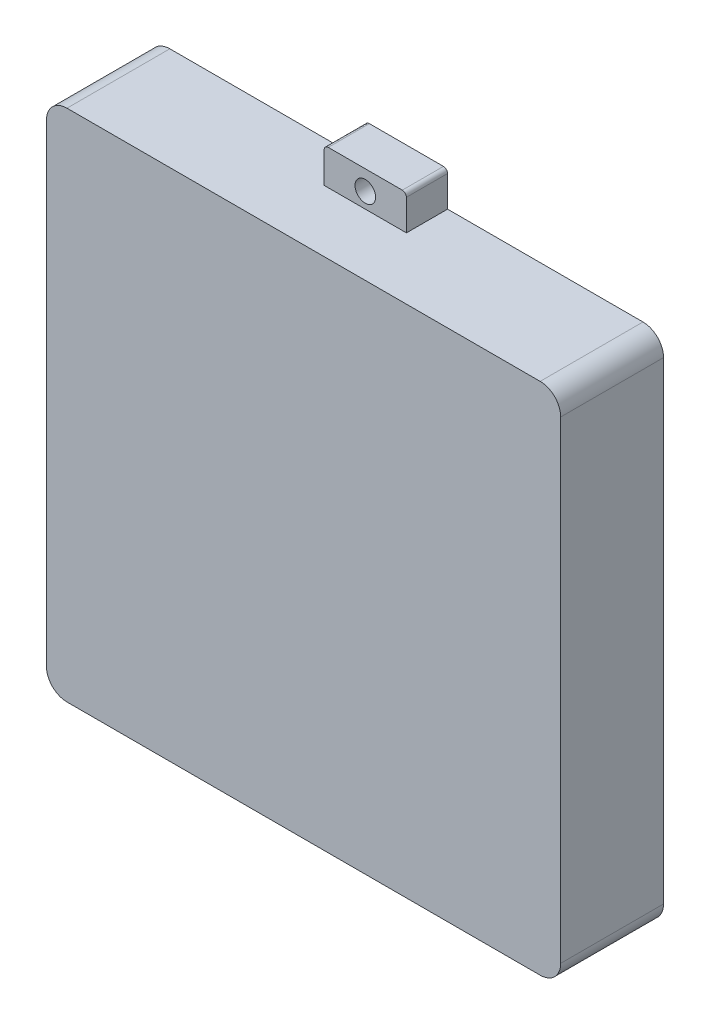
SolidWorks part; units mm, degrees
ref_plane "Front Plane" through (0, 0, 0) normal (0, 0, 1) x (1, 0, 0)
ref_plane "Top Plane" through (0, 0, 0) normal (0, 1, 0) x (1, 0, 0)
ref_plane "Right Plane" through (0, 0, 0) normal (1, 0, 0) x (0, 0, -1)
sketch "Sketch1" plane through (0, 0, 0) normal (0, 0, 1) x (1, 0, 0)
  line L1 (0, 0) -> (250, 0)
  line L2 (0, 0) -> (0, 250)
  line L3 (0, 250) -> (250, 250)
  line L4 (250, 0) -> (250, 250)
  dimension "D1" = 250
  dimension "D2" = 250
extrude "Boss-Extrude1" add sketch "Sketch1" along normal blind 50
sketch "Sketch2" plane through (0, 0, 0) normal (0, 0, 1) x (1, 0, 0)
  line L0 (0, 0) -> (250, 0) construction
  line L2 (105, 0) -> (105, -15)
  line L3 (107, -17) -> (143, -17)
  line L4 (145, 0) -> (145, -15)
  line L5 (0, 0) -> (250, 0) construction
  line L7 (145, 0) -> (105, 0)
  arc A0 (145, -15) -> (143, -17) centre (143, -15) cw
  arc A1 (107, -17) -> (105, -15) centre (107, -15) cw
  point P12 (125, 0)
  point P13 (125, -17)
  dimension "D1" = 2
  dimension "D2" = 20
  dimension "D3" = 15
  dimension "D4" = 20
extrude "Boss-Extrude2" add sketch "Sketch2" along normal blind 20
ref_plane "Plane1" through (0, 125, 0) normal (0, 1, 0) x (1, 0, 0)
mirror "Mirror1" about plane through (0, 125, 0) normal (0, 1, 0) of "Boss-Extrude2"
sketch "Sketch3" plane through (0, 0, 0) normal (0, 0, -1) x (-1, 0, 0)
  line L0 (-145, -7.5) -> (-105, -7.5) construction
  line L1 (-145, -15) -> (-145, 0) construction
  line L2 (-105, 0) -> (-105, -15) construction
  line L3 (27.5, 125) -> (-27.5, 125) construction
  circle A0 centre (-125, -7.5) radius 5
  circle A1 centre (-125, 257.5) radius 5
  point P8 (0, 0)
  dimension "D1" = 10
  dimension "D2" = 20
extrude "Cut-Extrude1" cut sketch "Sketch3" against normal blind 25
sketch "Sketch5" plane through (0, 0, 0) normal (0, 0, -1) x (-1, 0, 0)
  line L0 (-246, 246) -> (-246, 4)
  line L5 (-246, 4) -> (-4, 4)
  line L6 (-4, 246) -> (-4, 4)
  line L7 (-246, 246) -> (-4, 246)
extrude "Cut-Extrude2" cut sketch "Sketch5" against normal blind 46
fillet "Fillet1" radius 10 4 edges at (250, 250, 25) (250, 0, 25) (0, 0, 25) (0, 250, 25)
fillet "Fillet2" radius 10 4 edges at (246, 4, 23) (246, 246, 23) (4, 4, 23) (4, 246, 23)
